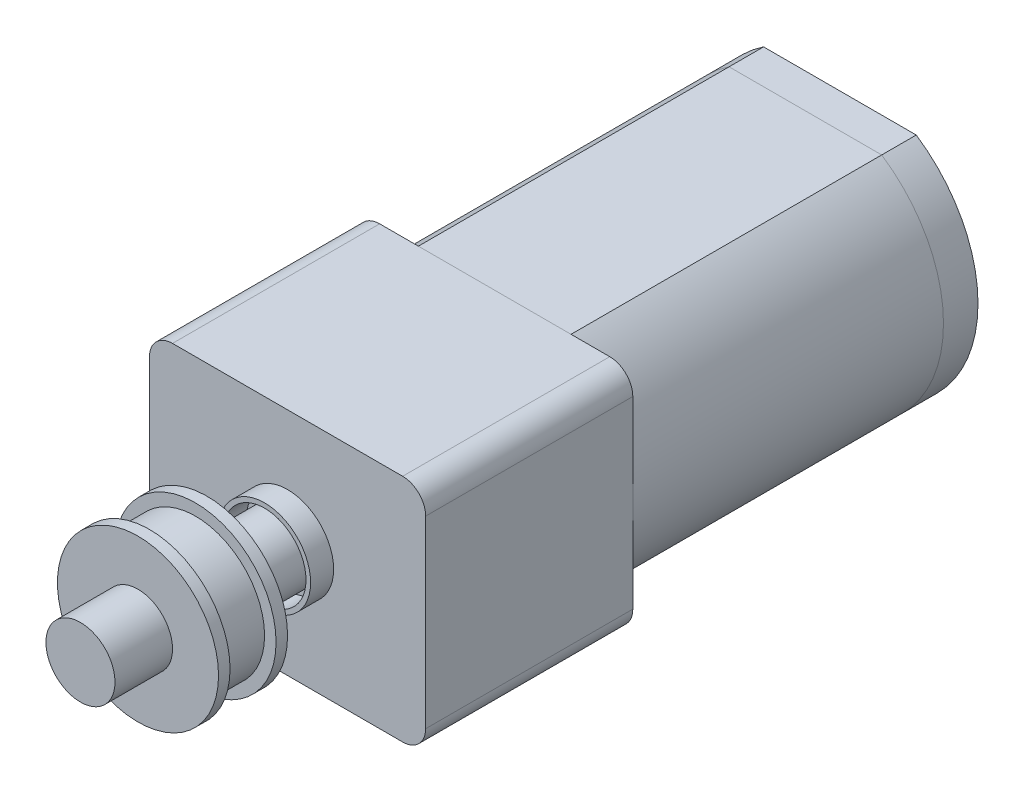
SolidWorks part; units mm, degrees
ref_plane "Front Plane" through (0, 0, 0) normal (0, 0, 1) x (1, 0, 0)
ref_plane "Top Plane" through (0, 0, 0) normal (0, 1, 0) x (1, 0, 0)
ref_plane "Right Plane" through (0, 0, 0) normal (1, 0, 0) x (0, 0, -1)
sketch "Sketch1" plane through (0, 0, 0) normal (0, 0, 1) x (1, 0, 0)
  line L1 (3.3166, -5) -> (-3.3166, -5)
  line L2 (3.3166, -5) -> (3.3166, 5)
  line L3 (3.3166, 5) -> (-3.3166, 5)
  line L4 (-3.3166, -5) -> (-3.3166, 5)
  line L5 (3.3166, -5) -> (-3.3166, 5) construction
  line L6 (3.3166, 5) -> (-3.3166, -5) construction
  arc A0 (-3.3166, 5) -> (-3.3166, -5) centre (0, 0) ccw
  arc A1 (3.3166, -5) -> (3.3166, 5) centre (0, 0) ccw
  dimension "D1" = 12
  dimension "D2" = 10
extrude "Boss-Extrude1" add sketch "Sketch1" along normal blind 13.5 contours L4 A0 | L2 A1 | L4 L1 L2 L3
sketch "Sketch2" plane through (0, 0, 13.5) normal (0, 0, 1) x (1, 0, 0)
  line L0 (3.3166, 5) -> (-3.3166, 5) construction
  line L1 (6, -5) -> (-6, -5)
  line L2 (6, -5) -> (6, 5)
  line L3 (6, 5) -> (-6, 5)
  line L4 (-6, -5) -> (-6, 5)
  line L5 (6, -5) -> (-6, 5) construction
  line L6 (6, 5) -> (-6, -5) construction
  point P0 (0, 0)
  dimension "D1" = 12
extrude "Boss-Extrude3" add sketch "Sketch2" along normal blind 9 separate body
sketch "Sketch4" plane through (0, 0, 22.5) normal (0, 0, 1) x (1, 0, 0)
  circle A0 centre (0, 0) radius 2
  circle A1 centre (0, 0) radius 1.8
  dimension "D1" = 4
  dimension "D2" = 3.6
extrude "Boss-Extrude4" add sketch "Sketch4" along normal blind 1
sketch "Sketch5" plane through (0, 0, 22.5) normal (0, 0, 1) x (1, 0, 0)
  circle A0 centre (0, 0) radius 1.5
  dimension "D1" = 3
extrude "Boss-Extrude5" add sketch "Sketch5" along normal blind 9 separate body
sketch "Sketch6" plane through (0, 0, 0) normal (0, 0, -1) x (-1, 0, 0)
  line L4 (3.3166, 5) -> (-3.3166, 5)
  line L5 (-3.3166, -5) -> (3.3166, -5)
  line L6 (3.3166, 5) -> (-3.3166, 5)
  line L7 (-3.3166, -5) -> (3.3166, -5)
  arc A4 (3.3166, -5) -> (3.3166, 5) centre (0, 0) ccw
  arc A5 (-3.3166, 5) -> (-3.3166, -5) centre (0, 0) ccw
  arc A6 (3.3166, -5) -> (3.3166, 5) centre (0, 0) ccw
  arc A7 (-3.3166, 5) -> (-3.3166, -5) centre (0, 0) ccw
  dimension "D1" = 0
extrude "Boss-Extrude6" add sketch "Sketch6" along normal blind 1.5 separate body
sketch "Sketch7" plane through (0, 0, -1.5) normal (0, 0, -1) x (-1, 0, 0)
  circle A0 centre (0, 0) radius 2.5
  circle A1 centre (0, 0) radius 1.5
  dimension "D1" = 5
  dimension "D2" = 3
extrude "Boss-Extrude7" add sketch "Sketch7" along normal blind 1.5
fillet "Fillet1" radius 1 4 edges at (6, -5, 18) (-6, -5, 18) (-6, 5, 18) (6, 5, 18)
sketch "Sketch8" plane through (0, 0, 0) normal (0, 1, 0) x (1, 0, 0)
  line L0 (0, -31.5) -> (0, -24.6267) construction
  line L1 (0, -29) -> (3.5, -29)
  line L2 (0, -29) -> (0, -26)
  line L3 (0, -26) -> (3.5, -26)
  line L5 (-1.5, -31.5) -> (1.5, -31.5) construction
  line L6 (3.5, -26) -> (3.5, -26.5)
  line L7 (0, -27.5) -> (3, -27.5) construction
  line L8 (3.5, -26.5) -> (3, -26.5)
  line L9 (3, -26.5) -> (3, -28.5)
  line L10 (3.5, -28.5) -> (3, -28.5)
  line L11 (3.5, -28.5) -> (3.5, -29)
  point P15 (3, -27.5)
  point P16 (3, -28)
  dimension "D1" = 3
  dimension "D2" = 3.5
  dimension "D3" = 2.5
  dimension "D4" = 2
  dimension "D5" = 0.5
revolve "Revolve1" add sketch "Sketch8" angle 360 about L0
